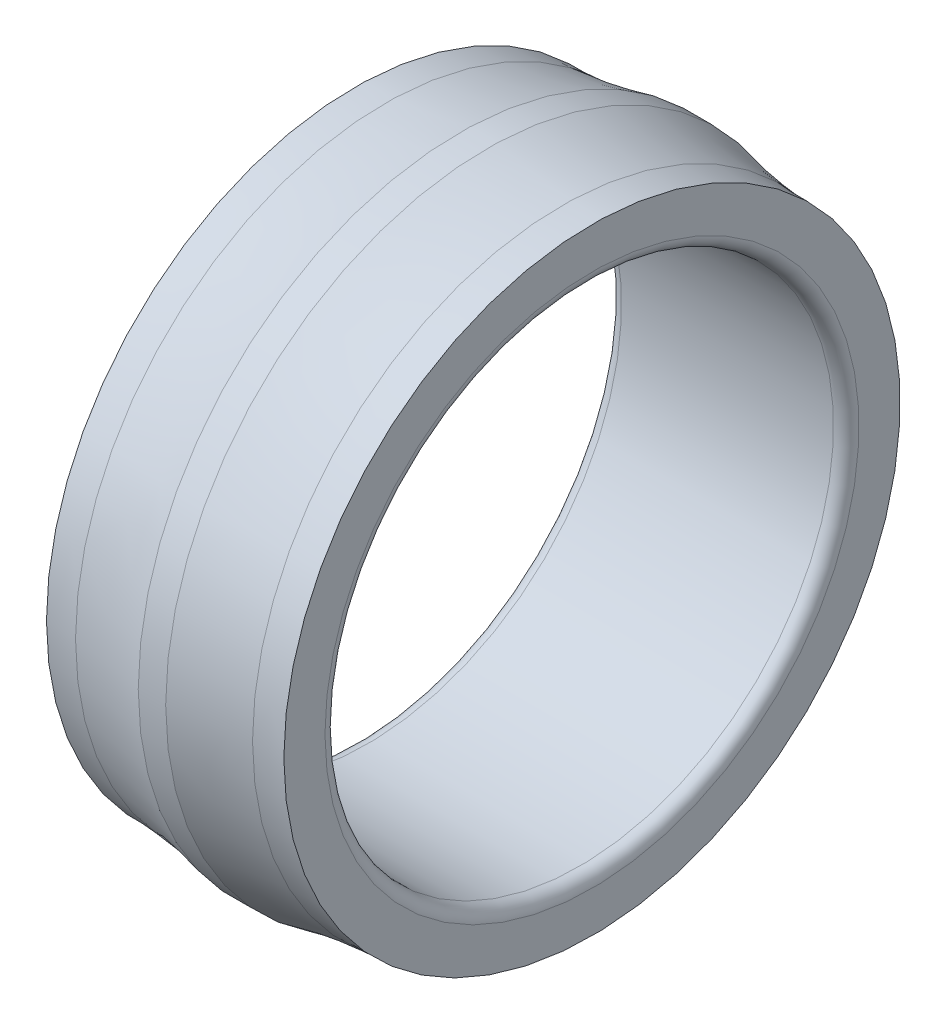
SolidWorks part; units mm, degrees
ref_plane "Front Plane" through (0, 0, 0) normal (0, 0, 1) x (1, 0, 0)
ref_plane "Top Plane" through (0, 0, 0) normal (0, 1, 0) x (1, 0, 0)
ref_plane "Right Plane" through (0, 0, 0) normal (1, 0, 0) x (0, 0, -1)
ref_plane "Plane1" through (0, 0, 0) normal (0, 0, 1) x (1, 0, 0)
sketch "Sketch1" plane through (0, 0, 0) normal (0, 0, 1) x (1, 0, 0)
  line L0 (1.5, 30) -> (26.5, 30)
  line L1 (28, 31.5) -> (28, 36.35)
  line L2 (15.6179, 37.9076) -> (12.3821, 37.9076)
  line L3 (0, 36.35) -> (0, 31.5)
  line L4 (28, 0) -> (-28, 0) construction
  arc A0 (0, 31.5) -> (1.5, 30) centre (1.5, 31.5) ccw
  arc A1 (26.5, 30) -> (28, 31.5) centre (26.5, 31.5) ccw
  arc A2 (28, 36.35) -> (24.4392, 36.4841) centre (27.2712, 64.3405) cw
  arc A3 (24.4392, 36.4841) -> (15.6179, 37.9076) centre (27.8846, 85.8801) cw
  arc A4 (12.3821, 37.9076) -> (3.5608, 36.4841) centre (0.1154, 85.8801) cw
  arc A5 (3.5608, 36.4841) -> (0, 36.35) centre (0.7288, 64.3405) cw
revolve "Revolve1" add sketch "Sketch1" angle 360 about L4
